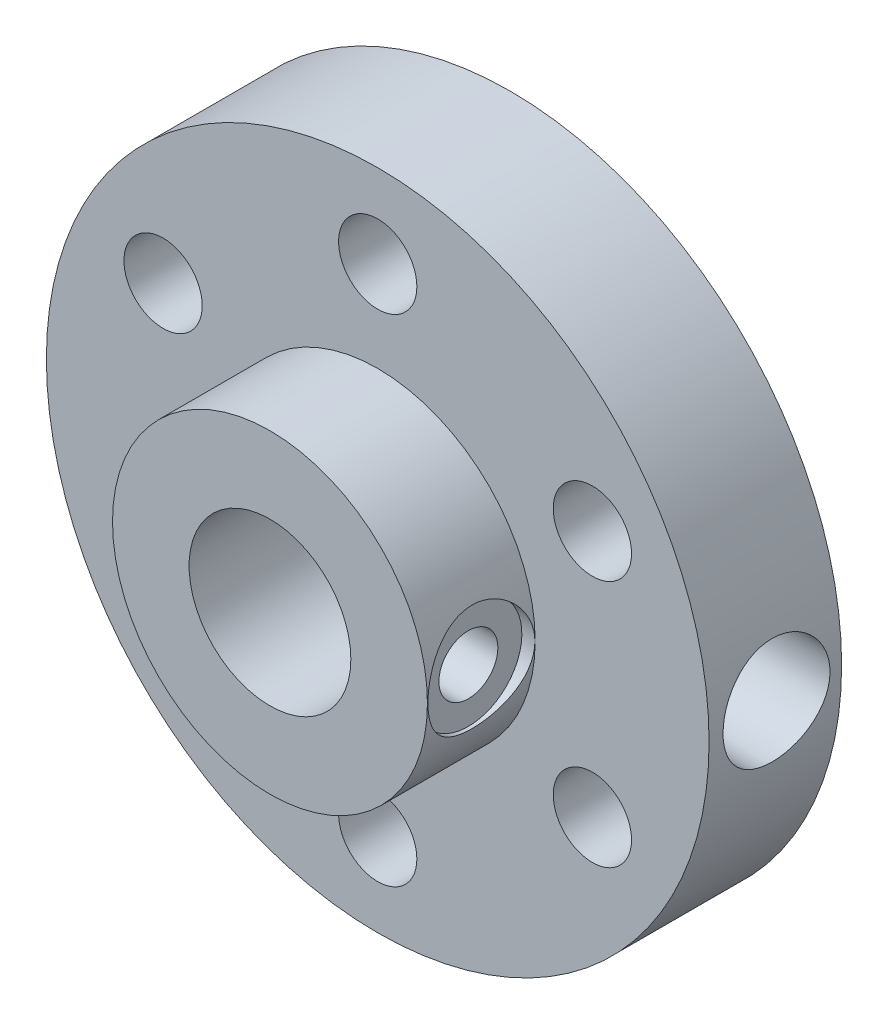
SolidWorks part; units mm, degrees
ref_plane "Front Plane" through (0, 0, 0) normal (0, 0, 1) x (1, 0, 0)
ref_plane "Top Plane" through (0, 0, 0) normal (0, 1, 0) x (1, 0, 0)
ref_plane "Right Plane" through (0, 0, 0) normal (1, 0, 0) x (0, 0, -1)
sketch "Sketch1" plane through (0, 0, 0) normal (0, 0, 1) x (1, 0, 0)
  circle A0 centre (0, 0) radius 12.7
extrude "Boss-Extrude1" add sketch "Sketch1" along normal blind 5.08
sketch "Sketch2" plane through (0, 0, 5.08) normal (0, 0, 1) x (1, 0, 0)
  circle A0 centre (0, 0) radius 6.035
  point P3 (6.035, 0)
extrude "Boss-Extrude2" add sketch "Sketch2" along normal blind 4.13
sketch "Sketch9" plane through (0, 0, 5.08) normal (0, 0, 1) x (1, 0, 0)
  line L0 (0, 0) -> (0.2211, 9.5274) construction
sketch "Sketch3" plane through (0, 0, 9.21) normal (0, 0, 1) x (1, 0, 0)
  circle A0 centre (0, 0) radius 3.1
extrude "Cut-Extrude1" cut sketch "Sketch3" against normal up to next
sketch "Sketch12" plane through (0, 0, 5.08) normal (0, 0, 1) x (1, 0, 0)
  circle A0 centre (0, 0) radius 9.53 construction
sketch "Sketch13" plane through (0, 0, 5.08) normal (0, 0, 1) x (1, 0, 0)
  circle A0 centre (0, 0) radius 12.7 construction
  point P0 (12.7, 0)
sketch "Sketch14" plane through (0, 0, 9.21) normal (0, 0, 1) x (1, 0, 0)
  circle A0 centre (0, 0) radius 6.035 construction
  point P0 (6.035, 0)
ref_plane "Plane1" through (12.7, 0, 5.08) normal (1, 0, 0) x (0, 0, -1)
ref_plane "Plane2" through (6.035, 0, 9.21) normal (1, 0, 0) x (0, 0, -1)
sketch "Sketch16" plane through (6.035, 0, 9.21) normal (1, 0, 0) x (0, 0, -1)
  line L0 (0, 0) -> (4.1381, 0) construction
  circle A0 centre (2.069, 0) radius 2.05
  point P4 (2.069, 0)
extrude "Cut-Extrude2" cut sketch "Sketch16" against normal blind 0.5
sketch "Sketch20" plane through (5.535, 0, 0) normal (1, 0, 0) x (0, 0, -1)
  circle A1 centre (-7.141, 0) radius 2.05
  circle A2 centre (-7.141, 0) radius 2.05
  circle A3 centre (-7.141, 0) radius 2.05
  circle A4 centre (-7.141, 0) radius 2.05
  dimension "D1" = 0
  dimension "D2" = 0
hole_wizard "#4-40 Tapped Hole3" positions "Sketch22" profile "Sketch23" tap size "#4-40" standard "ANSI Inch"
sketch "Sketch22" plane through (5.535, 0, 0) normal (1, 0, 0) x (0, 0, -1)
  point P0 (-7.141, 0)
sketch "Sketch23" plane through (5.535, 0, 7.141) normal (0, 1, 0) x (0, 0, -1)
  line L0 (0, 0) -> (0, 2.435)
  line L1 (0, 2.435) -> (1.1303, 2.435)
  line L2 (1.1303, 2.435) -> (1.1303, 0)
  line L5 (1.1303, 0) -> (0, 0)
  line L11 (0, -6.35) -> (0, 107.95) construction
  dimension "Thru Tap Drill Dia." = 2.2606
  dimension "Thru Tap Drill Depth" = 2.435
cosmetic thread "Hole Thread3" parameters "D2"=2.8448
sketch "Sketch24" plane through (12.7, 0, 5.08) normal (1, 0, 0) x (0, 0, -1)
  line L0 (0.0906, 0) -> (5.08, 0) construction
  circle A0 centre (2.5853, 0) radius 2.05
extrude "Cut-Extrude3" cut sketch "Sketch24" against normal blind 7.1
sketch "Sketch25" plane through (5.6, 0, 0) normal (1, 0, 0) x (0, 0, -1)
  line L0 (-4.5447, 0) -> (-0.4447, 0) construction
  circle A0 centre (-2.4947, 0) radius 2.05 construction
  point P5 (-2.4947, 0)
hole_wizard "#4-40 Tapped Hole4" positions "Sketch27" profile "Sketch28" tap size "#4-40" standard "ANSI Inch"
sketch "Sketch27" plane through (5.6, 0, 0) normal (1, 0, 0) x (0, 0, -1)
  point P0 (-2.4947, 0)
sketch "Sketch28" plane through (5.6, 0, 2.4947) normal (0, 1, 0) x (0, 0, -1)
  line L0 (0, 0) -> (0, 2.5)
  line L1 (0, 2.5) -> (1.1303, 2.5)
  line L2 (1.1303, 2.5) -> (1.1303, 0)
  line L5 (1.1303, 0) -> (0, 0)
  line L11 (0, -6.35) -> (0, 107.95) construction
  dimension "Thru Tap Drill Dia." = 2.2606
  dimension "Thru Tap Drill Depth" = 2.5
cosmetic thread "Hole Thread4" parameters "D2"=2.8448
sketch "Sketch29" plane through (0, 0, 5.08) normal (0, 0, 1) x (1, 0, 0)
  line L0 (0, 0) -> (0, 9.5) construction
  circle A0 centre (0, 9.5) radius 1.5
  circle A1 centre (8.2272, 4.75) radius 1.5
  circle A2 centre (8.2272, -4.75) radius 1.5
  circle A3 centre (0, -9.5) radius 1.5
  circle A4 centre (-8.2272, -4.75) radius 1.5
  circle A5 centre (-8.2272, 4.75) radius 1.5
  dimension "D3" = 3
  dimension "D1" = 9.5
  dimension "D2" = 0
  dimension "D5" = 9.5
  dimension "D4" = 6
extrude "Cut-Extrude4" cut sketch "Sketch29" against normal blind 10
